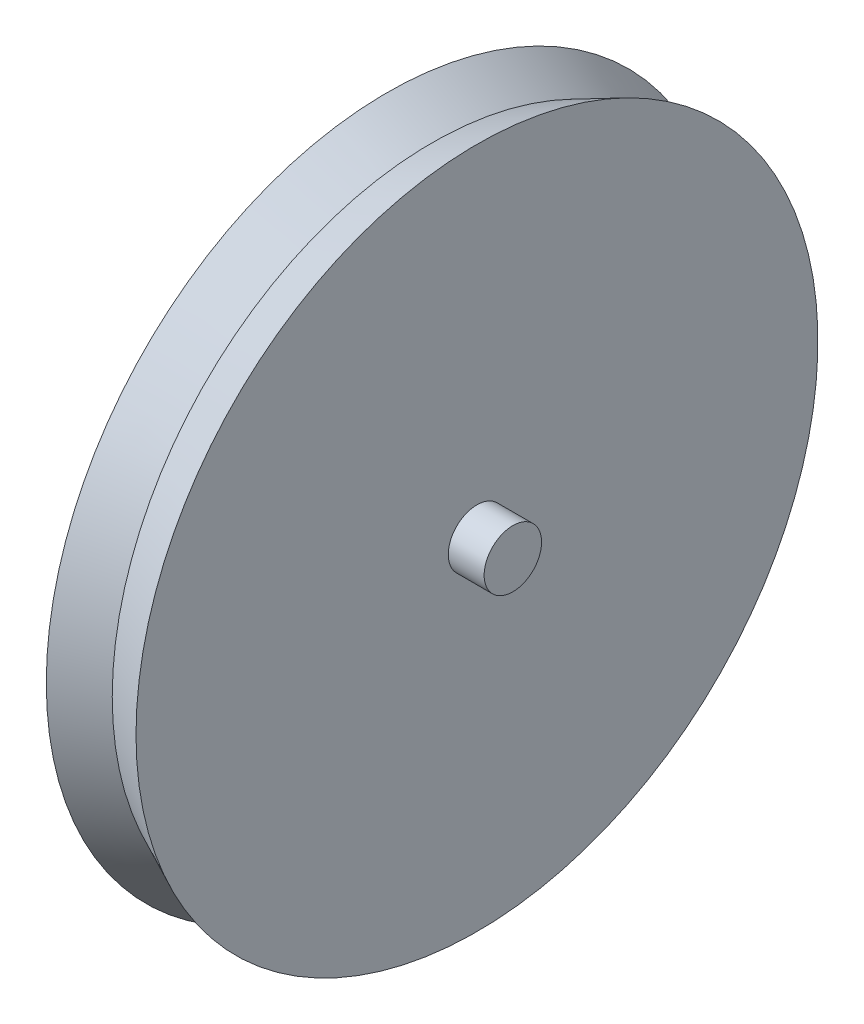
SolidWorks part; units mm, degrees
material "Nylon 101"
ref_plane "Front Plane" through (0, 0, 0) normal (0, 0, 1) x (1, 0, 0)
ref_plane "Top Plane" through (0, 0, 0) normal (0, 1, 0) x (1, 0, 0)
ref_plane "Right Plane" through (0, 0, 0) normal (1, 0, 0) x (0, 0, -1)
sketch "Sketch1" plane through (0, 0, 0) normal (0, 1, 0) x (1, 0, 0)
  line L0 (0, 0) -> (3.9688, 0) construction
  line L1 (3.9688, 0) -> (3.9688, 15.0812)
  line L2 (3.9688, 15.0812) -> (0, 15.0812) construction
  line L3 (0, 15.0812) -> (0, 0)
  line L4 (0, 15.0812) -> (1.9844, 14.1484)
  line L5 (1.9844, 14.1484) -> (3.9688, 15.0812)
  line L6 (0, 0) -> (3.9688, 0)
revolve "Revolve1" add sketch "Sketch1" angle 360 about L6
sketch "Sketch2" plane through (3.9688, 0, 0) normal (1, 0, 0) x (0, 0, -1)
  circle A2 centre (0, 0) radius 1.27
  point P2 (0, 0)
extrude "Boss-Extrude1" add sketch "Sketch2" along normal blind 1.5875 and the other way blind 5.5562 contours A2
